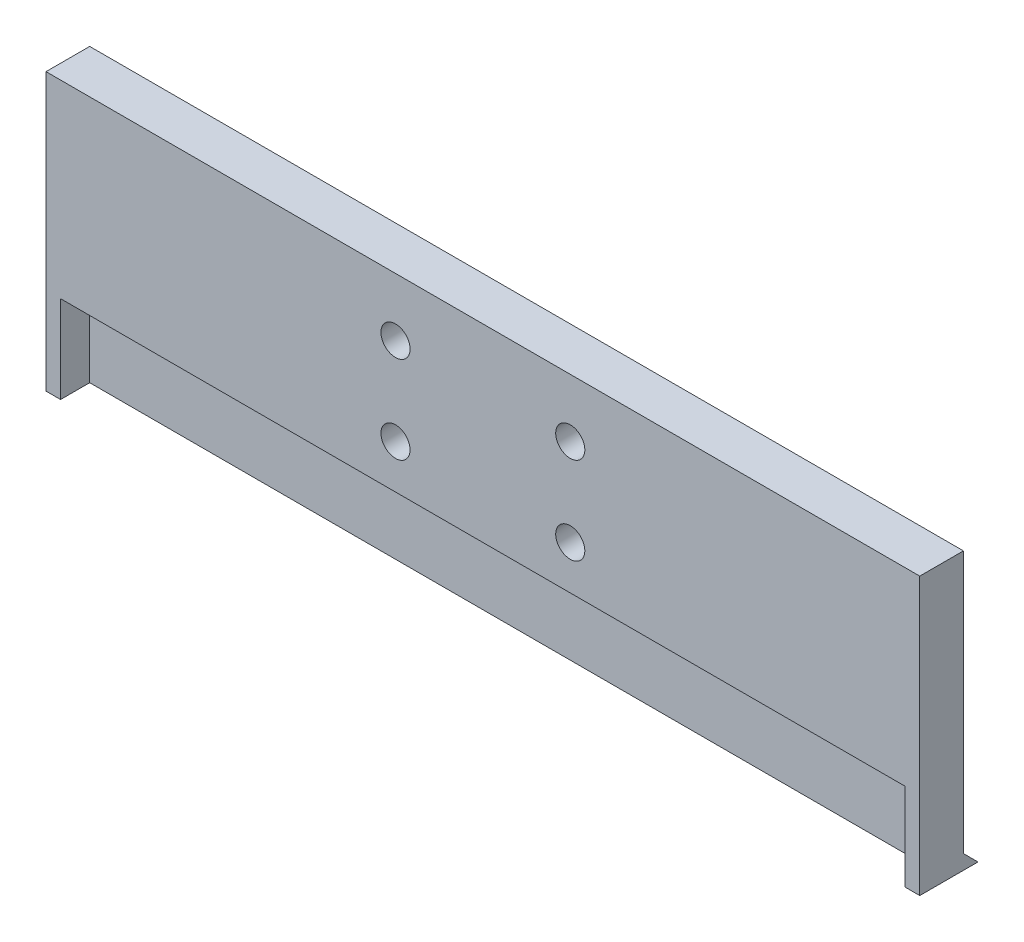
SolidWorks part; units mm, degrees
ref_plane "Plan de face" through (0, 0, 0) normal (0, 0, 1) x (1, 0, 0)
ref_plane "Plan de dessus" through (0, 0, 0) normal (0, 1, 0) x (1, 0, 0)
ref_plane "Plan de droite" through (0, 0, 0) normal (1, 0, 0) x (0, 0, -1)
sketch "Esquisse1" plane through (0, 0, 0) normal (0, 0, 1) x (1, 0, 0)
  line L1 (0, 0) -> (300, 0)
  line L2 (0, 0) -> (0, 95)
  line L3 (0, 95) -> (300, 95)
  line L4 (300, 0) -> (300, 95)
  dimension "D1" = 300
  dimension "D2" = 95
extrude "Boss.-Extru.1" add sketch "Esquisse1" along normal blind 5
sketch "Esquisse3" plane through (0, 0, 0) normal (-1, 0, 0) x (0, 0, 1)
  line L0 (0, 0) -> (-5, 0)
  line L1 (-5, 0) -> (0, 5)
  line L2 (0, 95) -> (0, 0) construction
  line L3 (0, 5) -> (0, 0)
  line M1 (0, 95) -> (0, 0)
  dimension "D1" = 5
  dimension "D2" = 5
extrude "Boss.-Extru.2" add sketch "Esquisse3" against normal up to surface (300 mm away) contours L1 L0 M1 up to face at (300, 47.5, 2.5)
sketch "Esquisse4" plane through (0, 0, 0) normal (0, 0, -1) x (-1, 0, 0)
  line L0 (-150, 95) -> (-150, -64.9747) construction
  line L1 (-300, 95) -> (0, 95) construction
  line L3 (-150, 95) -> (-195, 95)
  line L4 (-150, 95) -> (-150, 5)
  line L5 (-150, 5) -> (-195, 5)
  line L6 (-195, 95) -> (-195, 5)
  line L7 (-150, 5) -> (-105, 5)
  line L8 (-150, 5) -> (-150, 95)
  line L9 (-150, 95) -> (-105, 95)
  line L10 (-105, 5) -> (-105, 95)
  circle A0 centre (-180, 75) radius 5
  circle A1 centre (-180, 45) radius 5
  circle A2 centre (-120, 45) radius 5
  circle A3 centre (-120, 75) radius 5
  dimension "D3" = 10
  dimension "D4" = 10
  dimension "D5" = 10
  dimension "D6" = 10
  dimension "D7" = 20
  dimension "D8" = 30
  dimension "D9" = 20
  dimension "D10" = 30
  dimension "D11" = 30
  dimension "D12" = 30
  dimension "D13" = 30
  dimension "D14" = 30
  dimension "D1" = 45
  dimension "D2" = 45
  dimension "D15" = 90
sketch "Esquisse5" plane through (0, 0, 5) normal (0, 0, 1) x (1, 0, 0)
  line L0 (300, 0) -> (300, 95) construction
  line L1 (105, 95) -> (195, 95)
  line L3 (0, 0) -> (300, 0)
  line L4 (0, 0) -> (0, 95)
  line L5 (0, 0) -> (300, 0)
  line L6 (0, 0) -> (0, 30)
  line L7 (0, 95) -> (300, 95)
  line L8 (300, 0) -> (300, 30)
  line L9 (300, 0) -> (300, 95)
  line L10 (0, 95) -> (105, 95)
  line L11 (0, 95) -> (0, 30)
  line L16 (195, 95) -> (300, 95)
  line L17 (300, 30) -> (300, 95)
  line M5 (0, 95) -> (0, 0)
  line M6 (0, 0) -> (300, 0)
  line M7 (300, 0) -> (300, 95)
  line M8 (300, 95) -> (0, 95)
extrude "Boss.-Extru.3" add sketch "Esquisse5" along normal blind 10 contours L4 M8 M5 M6 M7
sketch "Esquisse6" plane through (0, 0, 0) normal (0, 0, -1) x (-1, 0, 0)
  circle A0 centre (-180, 75) radius 5
  circle A1 centre (-180, 45) radius 5
  circle A2 centre (-120, 45) radius 5
  circle A3 centre (-120, 75) radius 5
extrude "Enlèv. mat.-Extru.2" cut sketch "Esquisse6" against normal through all
sketch "Esquisse7" plane through (0, 0, 0) normal (0, -1, 0) x (1, 0, 0)
  line L0 (300, 0) -> (0, 0) construction
  line L1 (300, 15) -> (300, -5) construction
  line L2 (0, 15) -> (0, -5) construction
  line L3 (295, 28.0209) -> (5, 28.0209)
  line L4 (295, 28.0209) -> (295, 5)
  line L5 (295, 5) -> (5, 5)
  line L6 (5, 28.0209) -> (5, 5)
  dimension "D1" = 5
  dimension "D3" = 5
extrude "Enlèv. mat.-Extru.3" cut sketch "Esquisse7" against normal blind 30
